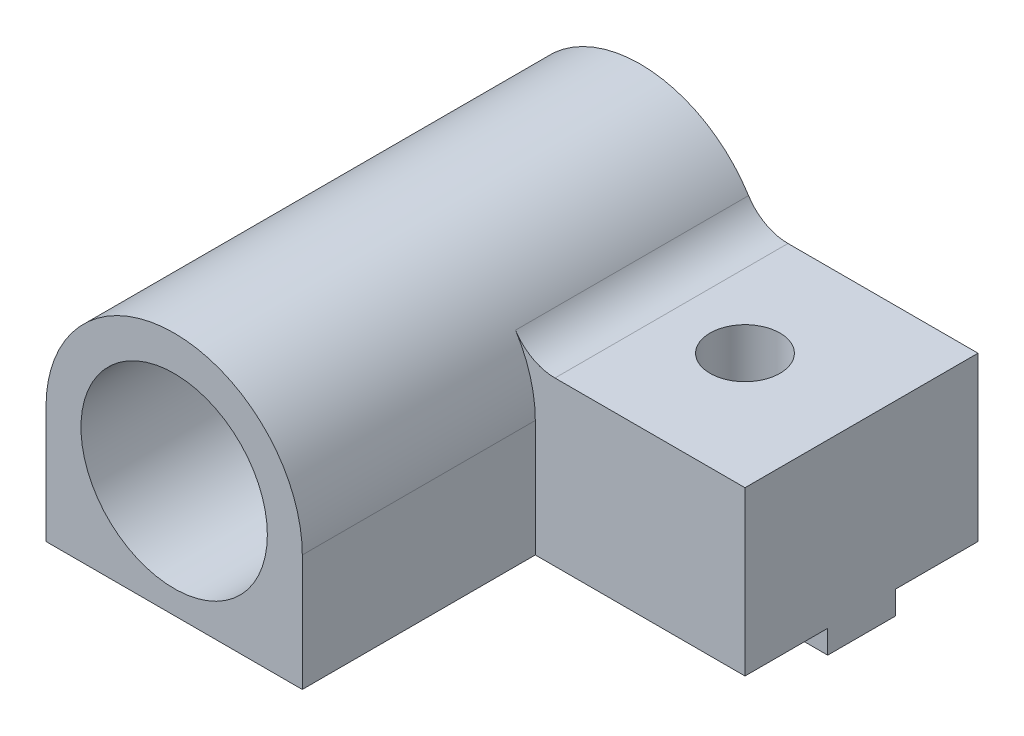
SolidWorks part; units mm, degrees
ref_plane "Front Plane" through (0, 0, 0) normal (0, 0, 1) x (1, 0, 0)
ref_plane "Top Plane" through (0, 0, 0) normal (0, 1, 0) x (1, 0, 0)
ref_plane "Right Plane" through (0, 0, 0) normal (1, 0, 0) x (0, 0, -1)
sketch "Sketch1" plane through (0, 0, 0) normal (0, 0, 1) x (1, 0, 0)
  line L0 (-5.5, 0) -> (-5.5, -5)
  line L1 (14.5, -5) -> (14.5, 2)
  line L3 (-5.5, -5) -> (14.5, -5)
  line L4 (14.5, 2) -> (5.1235, 2)
  arc A0 (-5.5, 0) -> (5.1235, 2) centre (0, 0) cw
  circle A1 centre (0, 0) radius 4
  dimension "D1" = 8
  dimension "D2" = 5.5
  dimension "D3" = 5
  dimension "D4" = 7
  dimension "D5" = 20
  dimension "D6" = 9.3765
extrude "Main" add sketch "Sketch1" along normal blind 10
sketch "Sketch3" plane through (0, -5, 0) normal (0, -1, 0) x (-1, 0, 0)
  line L0 (5.5, -10) -> (5.5, 0) construction
  line L1 (5.5, -6.45) -> (-14.5, -6.45)
  line L2 (5.5, -6.45) -> (5.5, -3.55)
  line L3 (5.5, -3.55) -> (-14.5, -3.55)
  line L4 (-14.5, -6.45) -> (-14.5, -3.55)
  line L5 (-14.5, -10) -> (-14.5, 0) construction
  line L6 (5.5, 0) -> (-14.5, 0) construction
  dimension "D1" = 2.9
  dimension "D2" = 3.55
extrude "MakerBeamRectangularGuide" add sketch "Sketch3" along normal blind 1
sketch "Sketch4" plane through (0, 2, 0) normal (0, 1, 0) x (1, 0, 0)
  line L0 (14.5, -10) -> (5.1235, -10) construction
  line L1 (14.5, -10) -> (14.5, 0) construction
  circle A0 centre (9.5, -5) radius 1.5
  dimension "D1" = 3
  dimension "D2" = 5
  dimension "D3" = 5
extrude "MakerBeamFixHole" cut sketch "Sketch4" against normal through all
fillet "Fillet1" radius 2 1 edges at (5.1235, 2, 5)
sketch "Sketch5" plane through (0, 0, 10) normal (0, 0, 1) x (1, 0, 0)
  line L0 (-5.5, -5) -> (5.5, -5)
  line L1 (-5.5, -5) -> (14.5, -5) construction
  line L2 (-5.5, -5) -> (-5.5, 0)
  line L3 (-5.5, 0) -> (-5.5, -5) construction
  line L4 (5.5, 0) -> (5.5, -5)
  arc A0 (5.5, 0) -> (-5.5, 0) centre (0, 0) ccw
  circle A1 centre (0, 0) radius 4
extrude "Boss-Extrude1" add sketch "Sketch5" along normal blind 10
